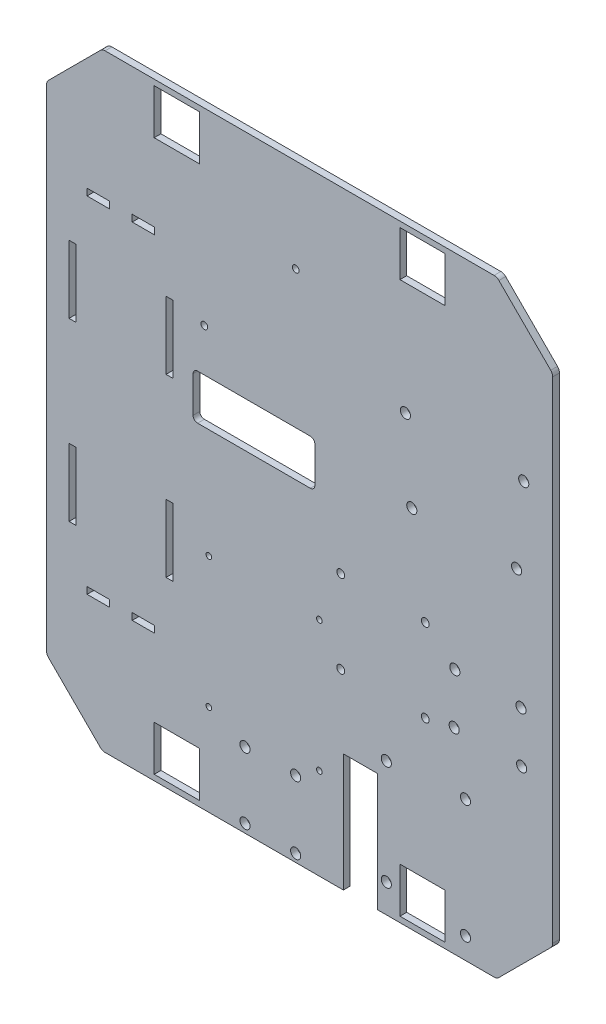
SolidWorks part; units mm, degrees
material "Alliage 1060"
ref_plane "Plan de dessus" through (0, 0, 0) normal (0, 0, 1) x (1, 0, 0)
ref_plane "Plan de droite" through (0, 0, 0) normal (0, 1, 0) x (1, 0, 0)
ref_plane "Plan de face" through (0, 0, 0) normal (1, 0, 0) x (0, 0, -1)
sketch "Esquisse1" plane through (0, 0, 0) normal (0, 0, 1) x (1, 0, 0)
  line L0 (0, 0) -> (-175, 0)
  line L1 (-175, 0) -> (-199.7487, 24.7487)
  line L2 (-199.7487, 24.7487) -> (-199.7487, 244.7487)
  line L3 (-199.7487, 244.7487) -> (-175, 269.4975)
  line L4 (-175, 269.4975) -> (0, 269.4975)
  line L5 (0, 269.4975) -> (24.7487, 244.7487)
  line L6 (24.7487, 244.7487) -> (24.7487, 24.7487)
  line L7 (24.7487, 24.7487) -> (0, 0)
  dimension "D1" = 220
  dimension "D2" = 35
  dimension "D3" = 135
  dimension "D4" = 175
extrude "Base" add sketch "Esquisse1" along normal blind 3
sketch "Esquisse2" plane through (0, 0, 3) normal (0, 0, 1) x (1, 0, 0)
  line L0 (-87.5, 269.4975) -> (-87.5, 0) construction
  line L5 (0, 269.4975) -> (-175, 269.4975) construction
  line L6 (-175, 0) -> (0, 0) construction
  line L7 (-199.7487, 134.7487) -> (24.7487, 134.7487) construction
  line L8 (-199.7487, 244.7487) -> (-199.7487, 24.7487) construction
  line L9 (24.7487, 24.7487) -> (24.7487, 244.7487) construction
  line L10 (-152, 2.5) -> (-132, 22.5) construction
  line L11 (-152, 246.9975) -> (-132, 246.9975)
  line L12 (-152, 246.9975) -> (-152, 266.9975)
  line L13 (-152, 266.9975) -> (-132, 266.9975)
  line L14 (-132, 246.9975) -> (-132, 266.9975)
  line L15 (-152, 246.9975) -> (-132, 266.9975) construction
  line L16 (-152, 266.9975) -> (-132, 246.9975) construction
  line L17 (-152, 22.5) -> (-132, 2.5) construction
  line L18 (-152, 2.5) -> (-132, 2.5)
  line L19 (-152, 22.5) -> (-152, 2.5)
  line L20 (-152, 22.5) -> (-132, 22.5)
  line L21 (-132, 22.5) -> (-132, 2.5)
  line L22 (-23, 2.5) -> (-43, 2.5)
  line L23 (-23, 22.5) -> (-43, 22.5)
  line L24 (-43, 22.5) -> (-43, 2.5)
  line L25 (-23, 22.5) -> (-43, 2.5) construction
  line L26 (-23, 2.5) -> (-43, 22.5) construction
  line L27 (-23, 22.5) -> (-23, 2.5)
  line L28 (-43, 246.9975) -> (-43, 266.9975)
  line L29 (-23, 246.9975) -> (-43, 266.9975) construction
  line L30 (-23, 266.9975) -> (-43, 246.9975) construction
  line L31 (-23, 246.9975) -> (-43, 246.9975)
  line L32 (-23, 246.9975) -> (-23, 266.9975)
  line L33 (-23, 266.9975) -> (-43, 266.9975)
  point P0 (-142, 256.9975)
  dimension "D1" = 20
  dimension "D2" = 54.5
  dimension "D3" = 2.5
extrude "Enlèv. mat.-Extru.1" cut sketch "Esquisse2" against normal through all
fillet "Congé1" radius 3 8 edges at (-199.7487, 24.7487, 1.5) (-175, 0, 1.5) (0, 0, 1.5) (24.7487, 24.7487, 1.5) (24.7487, 244.7487, 1.5) (0, 269.4975, 1.5) (-175, 269.4975, 1.5) (-199.7487, 244.7487, 1.5)
sketch "Esquisse4" plane through (0, 0, 3) normal (0, 0, 1) x (1, 0, 0)
  line L5 (-82.7487, 166.9975) -> (-132.7487, 166.9975)
  line L8 (-80.7487, 164.9975) -> (-80.7487, 148.9975)
  line L9 (-82.7487, 146.9975) -> (-132.7487, 146.9975)
  line L11 (-23, 2.5) -> (-23, 22.5) construction
  line L12 (-43, 2.5) -> (-23, 2.5) construction
  line L13 (-134.7487, 164.9975) -> (-134.7487, 148.9975)
  line L14 (-199.7487, 243.5061) -> (-199.7487, 25.9914) construction
  circle A0 centre (-78.7487, 98.4975) radius 1.25
  circle A1 centre (-127.7487, 98.4975) radius 1.25
  circle A2 centre (-78.7487, 40.4975) radius 1.25
  circle A3 centre (-127.7487, 40.4975) radius 1.25
  circle A4 centre (-129.7487, 185.9975) radius 1.5
  circle A5 centre (-89.2487, 227.9975) radius 1.5
  arc A6 (-80.7487, 164.9975) -> (-82.7487, 166.9975) centre (-82.7487, 164.9975) ccw
  arc A7 (-82.7487, 146.9975) -> (-80.7487, 148.9975) centre (-82.7487, 148.9975) ccw
  arc A8 (-134.7487, 148.9975) -> (-132.7487, 146.9975) centre (-132.7487, 148.9975) ccw
  arc A9 (-134.7487, 164.9975) -> (-132.7487, 166.9975) centre (-132.7487, 164.9975) cw
  point P8 (-80.7487, 146.9975)
  dimension "D13" = 37.9975
  dimension "D2" = 65
  dimension "D3" = 55.7487
  dimension "D4" = 3
  dimension "D5" = 50
  dimension "D11" = 104.7487
  dimension "D9" = 2
  dimension "D10" = 2
extrude "Enlèv. mat.-Extru.4" cut sketch "Esquisse4" against normal through all
sketch "Esquisse5" plane through (0, 0, 3) normal (0, 0, 1) x (1, 0, 0)
  line L0 (-68.0934, 52.3226) -> (-53.0623, 52.3226)
  line L1 (-53.0623, 52.3226) -> (-53.0623, 0)
  line L2 (-173.7574, 0) -> (-1.2426, 0) construction
  line L3 (-53.0623, 0) -> (-68.0934, 0)
  line L4 (-68.0934, 0) -> (-68.0934, 52.3226)
  line L5 (24.7487, 25.9914) -> (24.7487, 243.5061) construction
  line L6 (-23, 2.5) -> (-23, 22.5) construction
  line L7 (-43, 2.5) -> (-23, 2.5) construction
  line L8 (-43, 246.9975) -> (-23, 246.9975) construction
  line L9 (-79.2513, 181.3816) -> (-79.2513, 125.3816) construction
  line L22 (-79.2513, 153.3816) -> (-38.4877, 153.3816) construction
  line L39 (-41, 246.9975) -> (-41, 215.8484) construction
  line L40 (-25, 246.9975) -> (-25, 215.8484) construction
  line L41 (-44.2513, 227.8816) -> (-41, 227.8816) construction
  line L50 (4.7487, 72.3816) -> (24.7487, 72.3816) construction
  line L51 (4.7487, 72.3816) -> (4.7487, -6.8318) construction
  line L52 (-111.7384, 3.8325) -> (-121.6077, 3.8325) construction
  line L53 (-121.6077, 3.8325) -> (-121.6077, 6.4524) construction
  line L54 (-18.656, 109.4514) -> (-18.656, 119.3207) construction
  line L55 (-18.656, 119.3207) -> (-16.0361, 119.3207) construction
  line L56 (-13.95, 61.9819) -> (-13.95, 86.9819) construction
  circle A0 centre (-111.7384, 3.8325) radius 2.25
  circle A1 centre (-89.2689, 3.5385) radius 2.25
  circle A2 centre (-89.2689, 33.4615) radius 2.25
  circle A3 centre (-111.7384, 33.1675) radius 2.25
  circle A4 centre (-49.05, 12.6409) radius 2.25
  circle A5 centre (-13.95, 9.5) radius 2.25
  circle A6 centre (-49.05, 59.1409) radius 2.25
  circle A7 centre (-13.95, 61.9819) radius 2.25
  circle A8 centre (8.7487, 161.8975) radius 2.25
  circle A9 centre (11.8897, 196.9975) radius 2.25
  circle A10 centre (-37.7513, 161.8975) radius 2.25
  circle A11 centre (-40.5922, 196.9975) radius 2.25
  circle A12 centre (-18.656, 109.4514) radius 2.25
  circle A13 centre (-18.95, 86.9819) radius 2.25
  circle A14 centre (10.9731, 86.9819) radius 2.25
  circle A15 centre (10.6791, 109.4514) radius 2.25
  dimension "D1" = 4.5
  dimension "D2" = 4.5
  dimension "D3" = 46.5
  dimension "D4" = 52.4819
  dimension "D5" = 3.1409
  dimension "D6" = 16
  dimension "D7" = 50
  dimension "D8" = 35.1
extrude "Enlèv. mat.-Extru.5" cut sketch "Esquisse5" against normal up to next
sketch "Esquisse7" plane through (0, 0, 3) normal (0, 0, 1) x (1, 0, 0)
  circle A0 centre (6.4987, 233.5269) radius 2
  circle A1 centre (6.4987, 218.3975) radius 2
  dimension "D1" = 4
sketch "cagetteù" plane through (0, 0, 3) normal (0, 0, 1) x (1, 0, 0)
  line L0 (-199.7487, 134.7487) -> (-189.7487, 134.7487) construction
  line L1 (-199.7487, 243.5061) -> (-199.7487, 25.9914) construction
  line L2 (-189.7487, 254.7487) -> (-189.7487, 14.7487) construction
  line L3 (-198.8701, 23.8701) -> (-175.8787, 0.8787) construction
sketch "PONT H mal place" plane through (0, 0, 3) normal (0, 0, 1) x (1, 0, 0)
  circle A0 centre (-69.2625, 120.9474) radius 1.75
  circle A1 centre (-69.2625, 84.2056) radius 1.75
  circle A2 centre (-31.7762, 84.2056) radius 1.75
  circle A3 centre (-31.7762, 120.9474) radius 1.75
  dimension "D1" = 3.5
extrude "pont_H_mal_place" cut sketch "PONT H mal place" against normal blind 3
sketch "Esquisse10" plane through (0, 0, 3) normal (0, 0, 1) x (1, 0, 0)
  line L0 (-181.7487, 56.7487) -> (-171.7487, 56.7487)
  line L1 (-171.7487, 56.7487) -> (-171.7487, 59.7487)
  line L2 (-171.7487, 59.7487) -> (-181.7487, 59.7487)
  line L3 (-181.7487, 59.7487) -> (-181.7487, 56.7487)
  line L4 (-186.7487, 80.7487) -> (-189.7487, 80.7487)
  line L5 (-189.7487, 80.7487) -> (-189.7487, 110.7487)
  line L6 (-189.7487, 110.7487) -> (-186.7487, 110.7487)
  line L7 (-186.7487, 110.7487) -> (-186.7487, 80.7487)
  line L8 (-151.7487, 56.7487) -> (-151.7487, 59.7487)
  line L9 (-151.7487, 59.7487) -> (-161.7487, 59.7487)
  line L10 (-161.7487, 59.7487) -> (-161.7487, 56.7487)
  line L11 (-161.7487, 56.7487) -> (-151.7487, 56.7487)
  line L12 (-143.7487, 80.7487) -> (-146.7487, 80.7487)
  line L13 (-146.7487, 80.7487) -> (-146.7487, 110.7487)
  line L14 (-146.7487, 110.7487) -> (-143.7487, 110.7487)
  line L15 (-143.7487, 110.7487) -> (-143.7487, 80.7487)
  line L16 (-186.7487, 158.7487) -> (-189.7487, 158.7487)
  line L17 (-189.7487, 158.7487) -> (-189.7487, 188.7487)
  line L18 (-186.7487, 158.7487) -> (-186.7487, 188.7487)
  line L19 (-186.7487, 188.7487) -> (-189.7487, 188.7487)
  line L20 (-161.7487, 209.7487) -> (-151.7487, 209.7487)
  line L21 (-151.7487, 209.7487) -> (-151.7487, 212.7487)
  line L22 (-151.7487, 212.7487) -> (-161.7487, 212.7487)
  line L23 (-161.7487, 212.7487) -> (-161.7487, 209.7487)
  line L24 (-171.7487, 209.7487) -> (-181.7487, 209.7487)
  line L25 (-181.7487, 209.7487) -> (-181.7487, 212.7487)
  line L26 (-181.7487, 212.7487) -> (-171.7487, 212.7487)
  line L27 (-171.7487, 212.7487) -> (-171.7487, 209.7487)
  line L28 (-143.7487, 158.7487) -> (-146.7487, 158.7487)
  line L29 (-146.7487, 158.7487) -> (-146.7487, 188.7487)
  line L30 (-146.7487, 188.7487) -> (-143.7487, 188.7487)
  line L31 (-143.7487, 188.7487) -> (-143.7487, 158.7487)
  line L32 (-189.7487, 158.7487) -> (-189.7487, 110.7487) construction
extrude "Enlèv. mat.-Extru.7" cut sketch "Esquisse10" against normal blind 3
